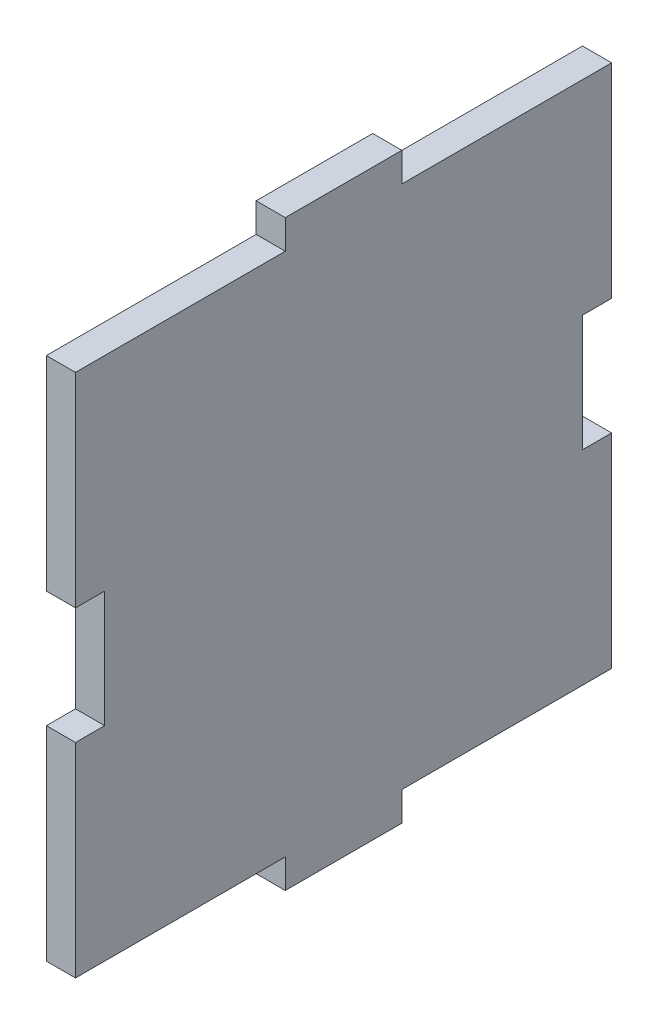
SolidWorks part; units mm, degrees
material "Acrylic (Medium-high impact)"
ref_plane "Front Plane" through (0, 0, 0) normal (0, 0, 1) x (1, 0, 0)
ref_plane "Top Plane" through (0, 0, 0) normal (0, 1, 0) x (1, 0, 0)
ref_plane "Right Plane" through (0, 0, 0) normal (1, 0, 0) x (0, 0, -1)
sketch "Sketch1" plane through (0, 0, 0) normal (1, 0, 0) x (0, 0, -1)
  line L0 (-29.21, 28.575) -> (-6.35, 28.575)
  line L1 (-6.35, 28.575) -> (-6.35, 31.75)
  line L2 (-6.35, 31.75) -> (6.35, 31.75)
  line L3 (6.35, 31.75) -> (6.35, 28.575)
  line L4 (6.35, 28.575) -> (29.21, 28.575)
  line L5 (29.21, 28.575) -> (29.21, 6.35)
  line L6 (29.21, 6.35) -> (26.035, 6.35)
  line L7 (26.035, 6.35) -> (26.035, -6.35)
  line L8 (26.035, -6.35) -> (29.21, -6.35)
  line L9 (29.21, -6.35) -> (29.21, -28.575)
  line L10 (29.21, -28.575) -> (6.35, -28.575)
  line L11 (6.35, -28.575) -> (6.35, -31.75)
  line L12 (6.35, -31.75) -> (-6.35, -31.75)
  line L13 (-6.35, -31.75) -> (-6.35, -28.575)
  line L14 (-6.35, -28.575) -> (-29.21, -28.575)
  line L15 (-29.21, -28.575) -> (-29.21, -6.35)
  line L16 (-29.21, -6.35) -> (-26.035, -6.35)
  line L17 (-26.035, -6.35) -> (-26.035, 6.35)
  line L18 (-26.035, 6.35) -> (-29.21, 6.35)
  line L19 (-29.21, 6.35) -> (-29.21, 28.575)
  line L20 (-26.035, 0) -> (0, 0) construction
  line L21 (0, 0) -> (0, 31.75) construction
  dimension "D1" = 12.7
  dimension "D2" = 3.175
  dimension "D3" = 12.7
  dimension "D4" = 58.42
  dimension "D5" = 63.5
extrude "Boss-Extrude1" add sketch "Sketch1" along normal blind 3.175
